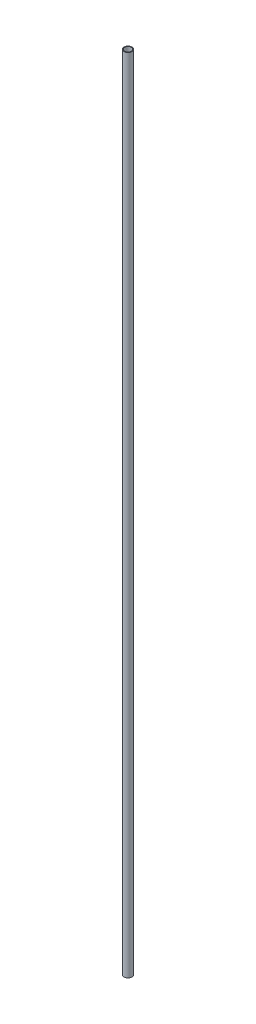
SolidWorks part; units mm, degrees
material "AISI 4130 Steel, annealed at 865C"
ref_plane "Front Plane" through (0, 0, 0) normal (0, 0, 1) x (1, 0, 0)
ref_plane "Top Plane" through (0, 0, 0) normal (0, 1, 0) x (1, 0, 0)
ref_plane "Right Plane" through (0, 0, 0) normal (1, 0, 0) x (0, 0, -1)
sketch "Sketch1" plane through (0, 0, 0) normal (0, 1, 0) x (1, 0, 0)
  circle A0 centre (0, 0) radius 38.1
  circle A1 centre (0, 0) radius 31.75
  dimension "D1" = 76.2
  dimension "D2" = 6.35
extrude "Boss-Extrude1" add sketch "Sketch1" along normal mid plane 7620
